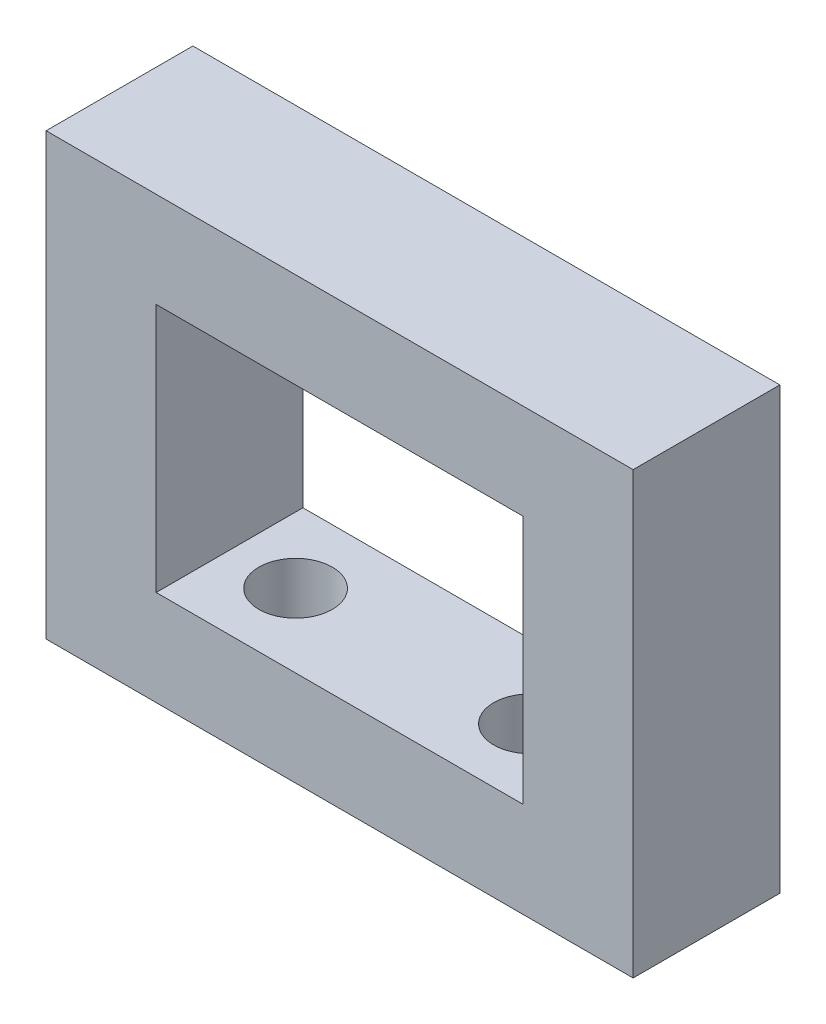
SolidWorks part; units mm, degrees
material "ABS"
ref_plane "前基準面" through (0, 0, 0) normal (0, 0, 1) x (1, 0, 0)
ref_plane "上基準面" through (0, 0, 0) normal (0, 1, 0) x (1, 0, 0)
ref_plane "右基準面" through (0, 0, 0) normal (1, 0, 0) x (0, 0, -1)
sketch "草圖1" plane through (0, 0, 0) normal (0, 0, 1) x (1, 0, 0)
  line L1 (-10, -7.5) -> (10, -7.5)
  line L2 (-10, -7.5) -> (-10, 7.5)
  line L3 (-10, 7.5) -> (10, 7.5)
  line L4 (10, -7.5) -> (10, 7.5)
  line L5 (-10, -7.5) -> (10, 7.5) construction
  line L6 (-10, 7.5) -> (10, -7.5) construction
  point P0 (0, 0)
  dimension "D1" = 20
  dimension "D2" = 15
extrude "填料-伸長1" add sketch "草圖1" along normal mid plane 5
sketch "草圖2" plane through (0, 0, 2.5) normal (0, 0, 1) x (1, 0, 0)
  line L1 (-6.25, -4.25) -> (6.25, -4.25)
  line L2 (-6.25, -4.25) -> (-6.25, 4.25)
  line L3 (-6.25, 4.25) -> (6.25, 4.25)
  line L4 (6.25, -4.25) -> (6.25, 4.25)
  line L5 (-6.25, -4.25) -> (6.25, 4.25) construction
  line L6 (-6.25, 4.25) -> (6.25, -4.25) construction
  point P0 (0, 0)
  dimension "D1" = 12.5
  dimension "D2" = 8.5
extrude "除料-伸長1" cut sketch "草圖2" against normal through all
sketch "草圖4" plane through (0, -7.5, 0) normal (0, -1, 0) x (1, 0, 0)
  line L0 (-4, 0) -> (4, 0) construction
  circle A0 centre (-4, 0) radius 1.25
  circle A1 centre (4, 0) radius 1.25
  point P3 (0, 0)
  dimension "D1" = 2.5
  dimension "D2" = 8
extrude "除料-伸長2" cut sketch "草圖4" against normal up to next
